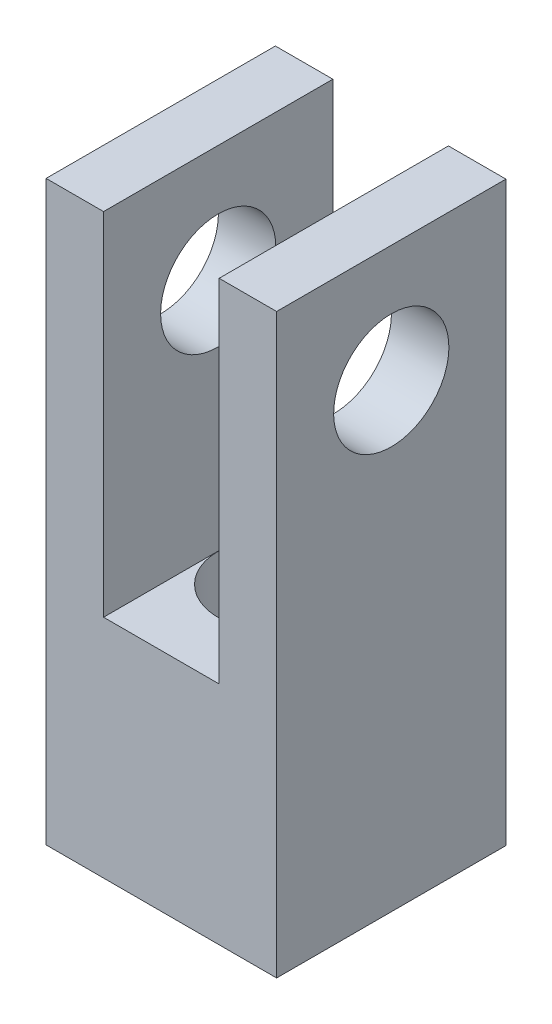
SolidWorks part; units mm, degrees
ref_plane "Front Plane" through (0, 0, 0) normal (0, 0, 1) x (1, 0, 0)
ref_plane "Top Plane" through (0, 0, 0) normal (0, 1, 0) x (1, 0, 0)
ref_plane "Right Plane" through (0, 0, 0) normal (1, 0, 0) x (0, 0, -1)
sketch "Sketch3" plane through (0, 0, 0) normal (0, 0, 1) x (1, 0, 0)
  line L0 (0, 0) -> (0, -19.0183) construction
  line L1 (2.3876, -9.6837) -> (-2.3876, -9.6837)
  line L2 (-2.3876, -9.6837) -> (-2.3876, 4.8324)
  line L3 (-2.3876, 4.8324) -> (-4.7625, 4.8324)
  line L4 (-4.7625, 4.8324) -> (-4.7625, -19.0183)
  line L5 (-4.7625, -19.0183) -> (4.7625, -19.0183)
  line L6 (-4.7625, 2.3813) -> (-2.3876, 2.3813) construction
  line L7 (-4.7625, -2.3813) -> (-2.3876, -2.3813) construction
  line L8 (-3.575, 2.3813) -> (-3.575, -2.3813) construction
  line L9 (3.575, 2.3813) -> (3.5751, -2.3812) construction
  line L10 (4.7625, -2.3812) -> (2.3876, -2.3812) construction
  line L11 (4.7625, 2.3813) -> (2.3876, 2.3813) construction
  line L12 (4.7625, 4.8324) -> (4.7625, -19.0183)
  line L13 (2.3876, 4.8324) -> (4.7625, 4.8324)
  line L14 (2.3876, -9.6837) -> (2.3876, 4.8324)
  point P14 (-3.5751, 0)
  point P25 (0, -9.6837)
  dimension "D1" = 9.525
  dimension "D2" = 23.8506
  dimension "D3" = 2.3749
  dimension "D4" = 14.5161
  dimension "D5" = 4.7625
  dimension "D6" = 2.4511
extrude "Boss-Extrude1" add sketch "Sketch3" along normal mid plane 9.4742
sketch "Sketch4" plane through (0, -19.0183, 0) normal (0, -1, 0) x (1, 0, 0)
  circle A0 centre (0, 0) radius 2.3813
  dimension "D1" = 4.7625
extrude "Cut-Extrude1" cut sketch "Sketch4" against normal up to next
sketch "Sketch5" plane through (4.7625, 0, 0) normal (1, 0, 0) x (0, 0, -1)
  circle A0 centre (0, 0) radius 2.3813
  dimension "D1" = 4.7625
extrude "Cut-Extrude2" cut sketch "Sketch5" against normal through all
